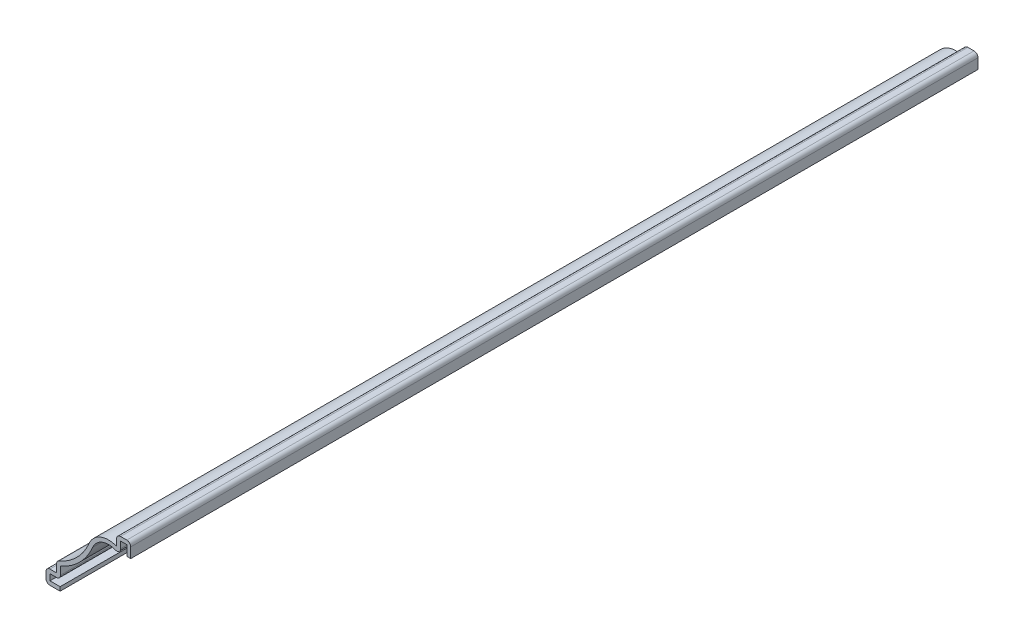
SolidWorks part; units mm, degrees
ref_plane "Front Plane" through (0, 0, 0) normal (0, 0, 1) x (1, 0, 0)
ref_plane "Top Plane" through (0, 0, 0) normal (0, 1, 0) x (1, 0, 0)
ref_plane "Right Plane" through (0, 0, 0) normal (1, 0, 0) x (0, 0, -1)
sketch "Sketch1" plane through (0, 0, 0) normal (0, 0, 1) x (1, 0, 0)
  line L0 (-15.875, 0) -> (0, 0) construction
  line L1 (0, 0) -> (0, 14.2875) construction
  line L2 (0, 14.2875) -> (0, 17.4625)
  line L3 (0, 17.4625) -> (-3.175, 17.4625)
  line L4 (-3.175, 17.4625) -> (-3.175, 15.0812)
  line L5 (-16.6687, 5.5563) -> (-16.6687, 3.175)
  line L6 (-16.6687, 3.175) -> (-19.05, 3.175)
  line L7 (-19.05, 3.175) -> (-19.05, 0)
  line L8 (-19.05, 0) -> (-15.875, 0)
  arc A0 (-3.175, 15.0812) -> (-9.385, 12.5303) centre (-4.9963, 10.6808) ccw
  arc A1 (-9.385, 12.5303) -> (-16.6687, 5.5563) centre (-21.0882, 17.4625) cw
  point P11 (-4.3427, 12.1412)
  point P15 (0, 0)
  point P16 (-12.5556, 0)
  point P17 (-4.3058, 6.6398)
  point P18 (-10.3055, 12.0849)
  point P19 (0, 0)
  point P20 (-9.5179, 12.3099)
  point P21 (0, 0)
  point P22 (0, 0)
  point P23 (0, 0)
  point P24 (0, 0)
  point P25 (0, 0)
  point P26 (-12.9169, 11.3913)
  point P27 (0, 0)
  point P28 (-21.6566, 17.4625)
  point P29 (0, 0)
  point P30 (0, 0)
  dimension "D10" = 4.7625
  dimension "D11" = 12.7
  dimension "D1" = 17.4625
  dimension "D2" = 19.05
  dimension "D3" = 3.175
  dimension "D4" = 3.175
  dimension "D5" = 3.175
  dimension "D6" = 3.175
  dimension "D7" = 2.3813
  dimension "D8" = 2.3813
  dimension "D9" = 2.3813
extrude "Extrude-Thin1" add sketch "Sketch1" against normal blind 190.5 thin thin type one direction reverse wall 0.889
fillet "Fillet1" radius 0.889 7 edges at (-3.175, 17.4625, -95.25) (-19.05, 0, -95.25) (-19.05, 3.175, -95.25) (-15.7797, 2.286, -95.25) (-16.6687, 5.5563, -95.25) (-2.286, 13.4481, -95.25) (0, 17.4625, -95.25)
